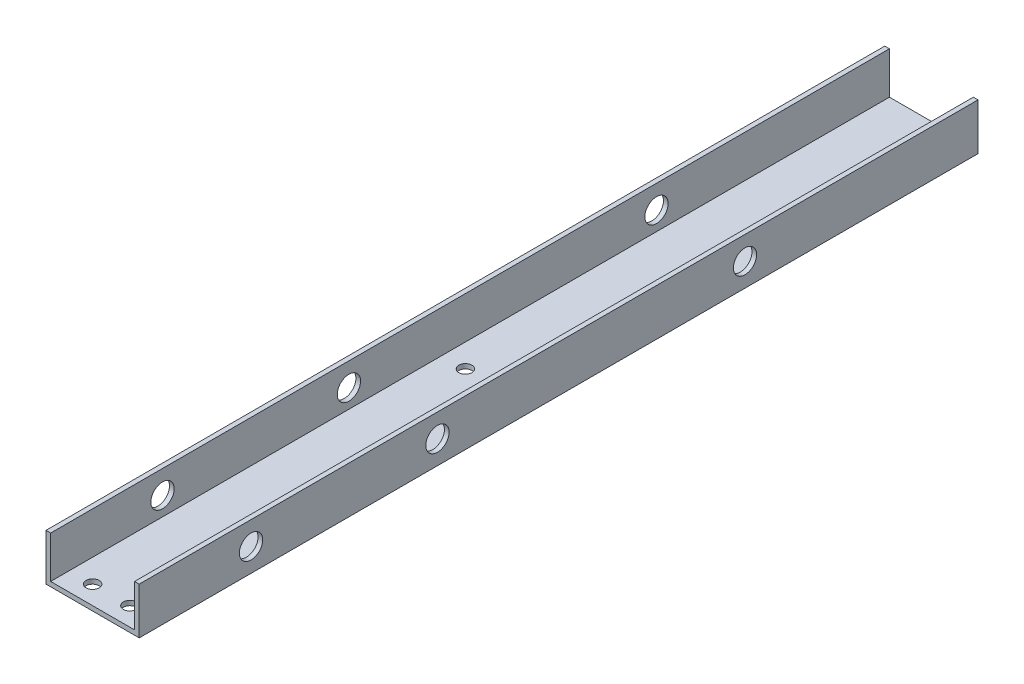
SolidWorks part; units mm, degrees
ref_plane "Front" through (0, 0, 0) normal (0, 0, 1) x (1, 0, 0)
ref_plane "Top" through (0, 0, 0) normal (0, 1, 0) x (1, 0, 0)
ref_plane "Right" through (0, 0, 0) normal (1, 0, 0) x (0, 0, -1)
sketch "Sketch1" plane through (0, 0, 0) normal (0, 0, 1) x (1, 0, 0)
  line L0 (48.26, 2.54) -> (48.26, 25.4)
  line L1 (0, 0) -> (50.8, 0)
  line L2 (0, 0) -> (0, 25.4)
  line L4 (50.8, 0) -> (50.8, 25.4)
  line L5 (2.54, 2.54) -> (48.26, 2.54)
  line L6 (2.54, 2.54) -> (2.54, 25.4)
  line L7 (50.8, 25.4) -> (48.26, 25.4)
  line L8 (0, 25.4) -> (2.54, 25.4)
  dimension "D1" = 25.4
  dimension "D2" = 50.8
  dimension "D3" = 2.54
extrude "Boss-Extrude1" add sketch "Sketch1" along normal blind 457.2
sketch "Sketch2" plane through (0, 0, 0) normal (0, -1, 0) x (1, 0, 0)
  line L0 (25.4, 457.2) -> (25.4, 437.2063) construction
  line L3 (0, 447.04) -> (15.24, 447.04) construction
  line L4 (15.24, 457.2) -> (15.24, 447.04) construction
  line L5 (0, 457.2) -> (50.8, 457.2) construction
  line L6 (0, 457.2) -> (0, 0) construction
  circle A1 centre (15.24, 447.04) radius 3.556
  circle A2 centre (35.56, 447.04) radius 3.556
  dimension "D1" = 10.16
  dimension "D2" = 15.24
extrude "Cut-Extrude1" cut sketch "Sketch2" against normal up to next
sketch "Sketch3" plane through (0, 0, 0) normal (0, -1, 0) x (1, 0, 0)
  line L0 (15.24, 447.04) -> (15.24, 243.84) construction
  line L1 (15.24, 447.04) -> (35.56, 447.04) construction
  line L2 (35.56, 447.04) -> (35.56, 243.84) construction
  line L3 (35.56, 243.84) -> (15.24, 243.84) construction
  circle A0 centre (15.24, 243.84) radius 3.556
  circle A1 centre (35.56, 243.84) radius 3.556
  circle A2 centre (15.24, 447.04) radius 3.556 construction
  dimension "D1" = 203.2
extrude "Cut-Extrude2" cut sketch "Sketch3" against normal up to next
sketch "Sketch4" plane through (0, 0, 0) normal (-1, 0, 0) x (0, 0, 1)
  line L0 (457.2, 12.7) -> (396.24, 12.7) construction
  line L1 (457.2, 25.4) -> (457.2, 0) construction
  line L2 (396.24, 12.7) -> (294.64, 12.7) construction
  line L4 (0, 12.7) -> (127, 12.7) construction
  line L5 (0, 25.4) -> (0, 0) construction
  circle A0 centre (396.24, 12.7) radius 6.35
  circle A1 centre (294.64, 12.7) radius 6.35
  circle A2 centre (127, 12.7) radius 6.35
  dimension "D2" = 12.7
  dimension "D4" = 127
  dimension "D1" = 60.96
  dimension "D3" = 101.6
extrude "Cut-Extrude3" cut sketch "Sketch4" against normal through all
